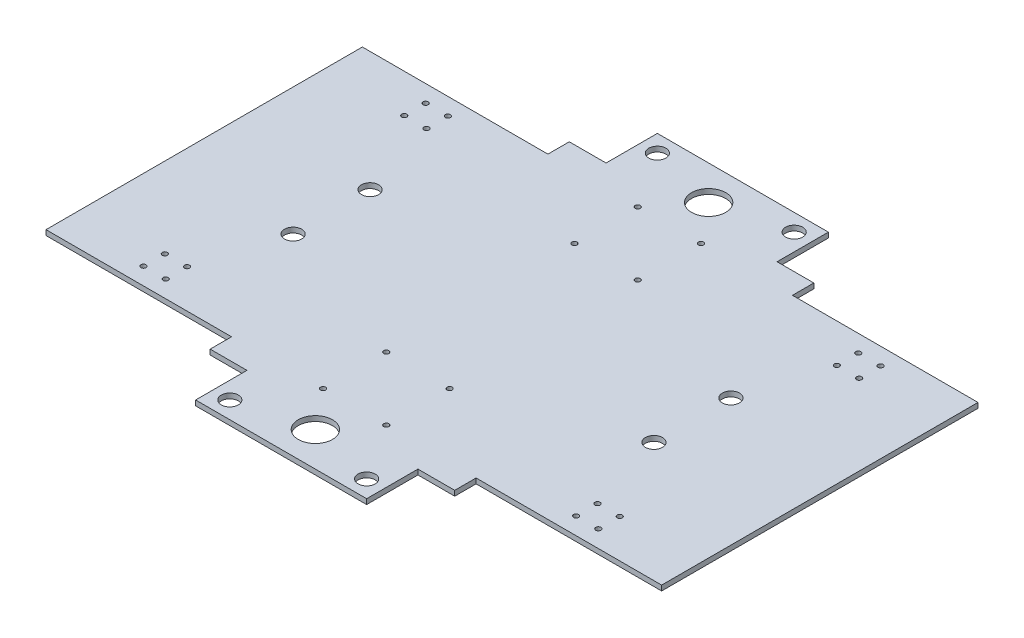
SolidWorks part; units mm, degrees
material "Acrylic (Medium-high impact)"
ref_plane "Front Plane" through (0, 0, 0) normal (0, 0, 1) x (1, 0, 0)
ref_plane "Top Plane" through (0, 0, 0) normal (0, 1, 0) x (1, 0, 0)
ref_plane "Right Plane" through (0, 0, 0) normal (1, 0, 0) x (0, 0, -1)
sketch "Sketch1" plane through (0, 0, 0) normal (0, 1, 0) x (1, 0, 0)
  line L0 (0, 86.435) -> (0, -88.6202) construction
  line L1 (-118.484, 0) -> (133.2945, 0) construction
  line L2 (-71.5, 92.5) -> (-180, 92.5)
  line L14 (180, 92.5) -> (180, -92.5)
  line L19 (-71.5, 92.5) -> (-71.5, 105)
  line L21 (71.5, 92.5) -> (71.5, 105)
  line L22 (71.5, 92.5) -> (180, 92.5)
  line L23 (-71.5, -92.5) -> (-180, -92.5)
  line L24 (-71.5, -92.5) -> (-71.5, -105)
  line L25 (71.5, -92.5) -> (71.5, -105)
  line L26 (71.5, -92.5) -> (180, -92.5)
  line L28 (-180, 92.5) -> (-180, -92.5)
  line L30 (50, -105) -> (50, -135)
  line L31 (50, -135) -> (-50, -135)
  line L32 (-50, -135) -> (-50, -105)
  line L33 (50, -105) -> (71.5, -105)
  line L34 (-71.5, -105) -> (-50, -105)
  line L35 (-71.5, 105) -> (-50, 105)
  line L36 (-50, 135) -> (-50, 105)
  line L37 (50, 135) -> (-50, 135)
  line L38 (50, 105) -> (50, 135)
  line L39 (50, 105) -> (71.5, 105)
  circle A0 centre (133, -70) radius 1.5
  circle A1 centre (120, -70) radius 1.5
  circle A2 centre (133, -82.5) radius 1.5
  circle A3 centre (120, -82.5) radius 1.5
  circle A4 centre (-120, -82.5) radius 1.5
  circle A5 centre (-133, -82.5) radius 1.5
  circle A6 centre (-120, -70) radius 1.5
  circle A7 centre (-133, -70) radius 1.5
  circle A8 centre (-133, 70) radius 1.5
  circle A9 centre (-120, 70) radius 1.5
  circle A10 centre (-133, 82.5) radius 1.5
  circle A11 centre (-120, 82.5) radius 1.5
  circle A12 centre (133, 82.5) radius 1.5
  circle A13 centre (120, 82.5) radius 1.5
  circle A14 centre (120, 70) radius 1.5
  circle A15 centre (133, 70) radius 1.5
  circle A16 centre (105.5, 22.5) radius 5
  circle A17 centre (105.5, -22.5) radius 5
  circle A18 centre (-105.5, -22.5) radius 5
  circle A19 centre (-105.5, 22.5) radius 5
  circle A24 centre (18.5, -55) radius 1.5
  circle A25 centre (-18.5, -55) radius 1.5
  circle A26 centre (18.5, -92) radius 1.5
  circle A27 centre (-18.5, -92) radius 1.5
  circle A29 centre (18.5, 92) radius 1.5
  circle A30 centre (-18.5, 92) radius 1.5
  circle A31 centre (-18.5, 55) radius 1.5
  circle A32 centre (18.5, 55) radius 1.5
  circle A34 centre (-40, -125) radius 5
  circle A35 centre (40, -125) radius 5
  circle A36 centre (40, 125) radius 5
  circle A37 centre (-40, 125) radius 5
  circle A38 centre (0, 115) radius 10
  circle A39 centre (0, -115) radius 10
  point P48 (-18.5, -55)
  point P49 (-71.5, 92.5)
  point P51 (-126.5, 76.25)
  point P63 (18.5, -55)
  point P65 (18.5, -92)
  point P67 (-18.5, -92)
  dimension "D2" = 10
  dimension "D6" = 50
  dimension "D8" = 105.5
  dimension "D18" = 126.5
  dimension "D9" = 120
  dimension "D17" = 82.5
  dimension "D1" = 20
  dimension "D3" = 3
  dimension "D4" = 18.5
  dimension "D5" = 40
  dimension "D7" = 71.5
  dimension "D10" = 133
  dimension "D11" = 180
  dimension "D12" = 18.5
  dimension "D13" = 22.5
  dimension "D14" = 55
  dimension "D15" = 70
  dimension "D16" = 76.25
  dimension "D19" = 92
  dimension "D20" = 92.5
  dimension "D21" = 105
  dimension "D22" = 125
  dimension "D23" = 135
extrude "Boss-Extrude2" add sketch "Sketch1" along normal blind 3
